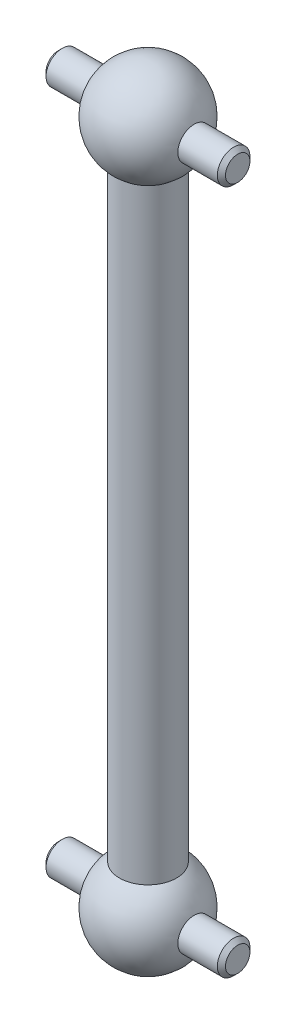
SolidWorks part; units mm, degrees
ref_plane "Plane1" through (0, 0, 0) normal (0, 0, 1) x (1, 0, 0)
ref_plane "Plane2" through (0, 0, 0) normal (0, 1, 0) x (1, 0, 0)
ref_plane "Plane3" through (0, 0, 0) normal (1, 0, 0) x (0, 0, -1)
sketch "Esquisse1" plane through (0, 0, 0) normal (0, 0, 1) x (1, 0, 0)
  line L0 (0, -3) -> (0, 45) construction
  line L1 (1.75, 39.5633) -> (1.75, 2.4367)
  line L2 (0, 45) -> (0, -3)
  arc A0 (1.75, 39.5633) -> (0, 45) centre (0, 42) ccw
  arc A1 (0, -3) -> (1.75, 2.4367) centre (0, 0) ccw
  dimension "D1" = 6
  dimension "D2" = 6
  dimension "D3" = 42
  dimension "D4" = 1.75
revolve "Base-Révolution" add sketch "Esquisse1" angle 360 about L0
sketch "Esquisse3" plane through (0, 0, 0) normal (1, 0, 0) x (0, 0, -1)
  line L0 (0, -3) -> (0, 45) construction
  circle A0 centre (0, 0) radius 1
  circle A1 centre (0, 42) radius 1
  dimension "D1" = 2
  dimension "D2" = 2
  dimension "D3" = 42
extrude "Boss.-Extru.1" add sketch "Esquisse3" along normal mid plane 11
chamfer "Chanfrein1" distance 0.25 angle 45
sketch "Esquisse4" plane through (0, 0, 0) normal (1, 0, 0) x (0, 0, -1)
  point P0 (0, 42)
